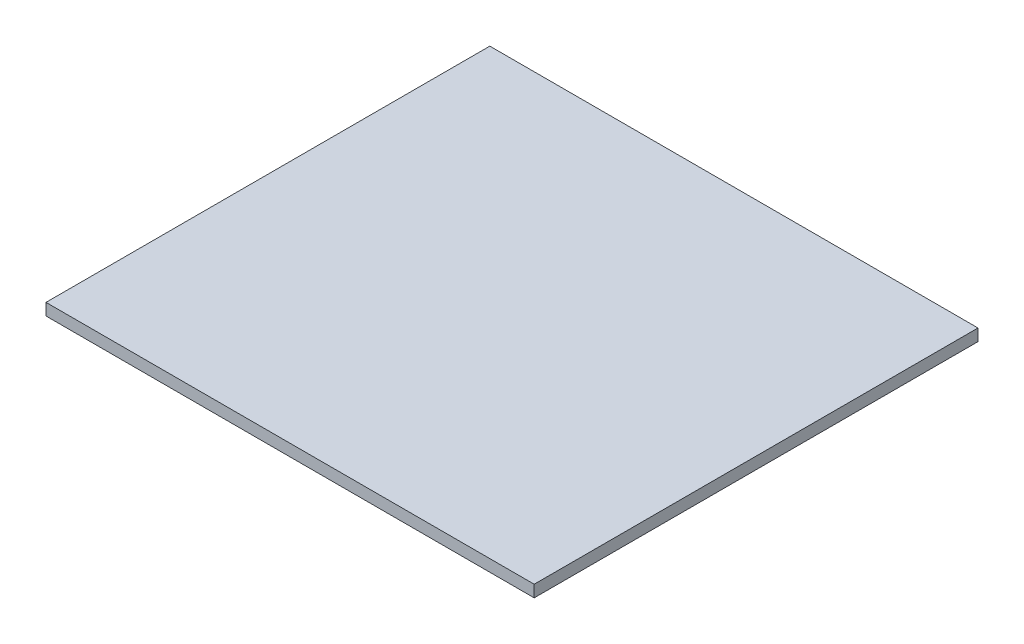
SolidWorks part; units mm, degrees
material "Cardboard"
ref_plane "Front Plane" through (0, 0, 0) normal (0, 0, 1) x (1, 0, 0)
ref_plane "Top Plane" through (0, 0, 0) normal (0, 1, 0) x (1, 0, 0)
ref_plane "Right Plane" through (0, 0, 0) normal (1, 0, 0) x (0, 0, -1)
sketch "Sketch1" plane through (0, 0, 0) normal (0, 1, 0) x (1, 0, 0)
  line L1 (0, 0) -> (165, 0)
  line L2 (0, 0) -> (0, 150)
  line L3 (0, 150) -> (165, 150)
  line L4 (165, 0) -> (165, 150)
  dimension "D1" = 150
  dimension "D2" = 165
extrude "Boss-Extrude1" add sketch "Sketch1" along normal blind 4
